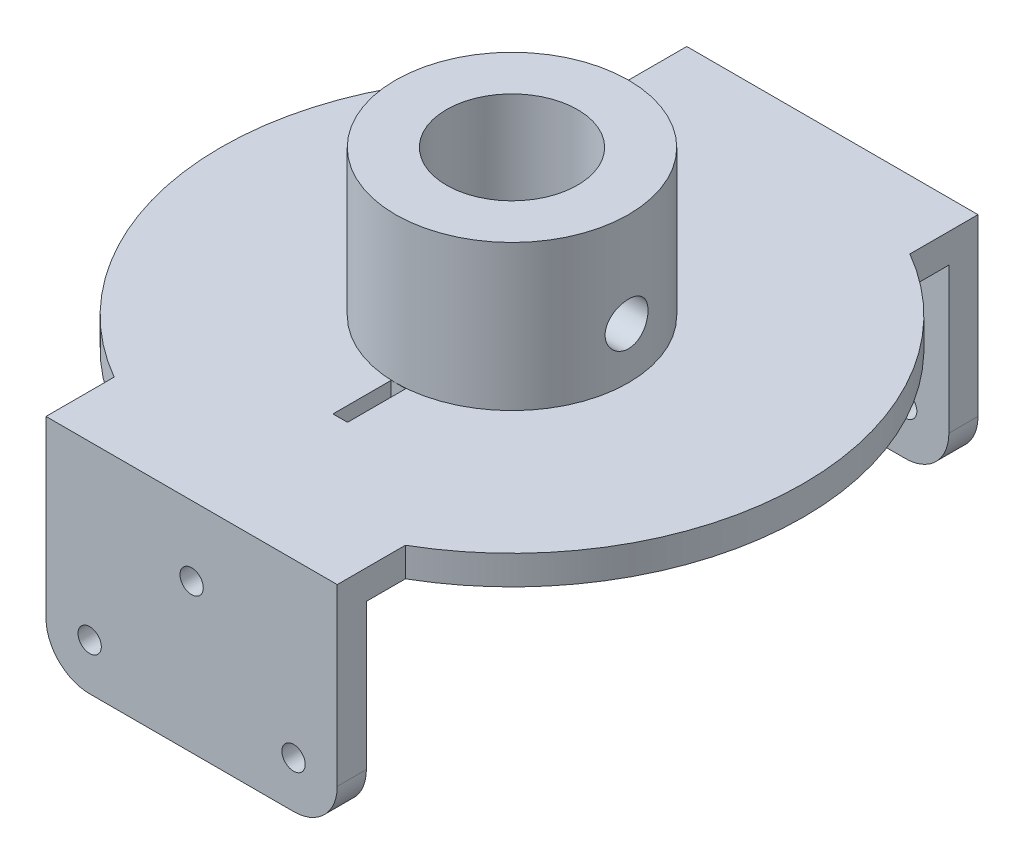
SolidWorks part; units mm, degrees
ref_plane "前视基准面" through (0, 0, 0) normal (0, 0, 1) x (1, 0, 0)
ref_plane "上视基准面" through (0, 0, 0) normal (0, 1, 0) x (1, 0, 0)
ref_plane "右视基准面" through (0, 0, 0) normal (1, 0, 0) x (0, 0, -1)
sketch "草图1" plane through (0, 0, 0) normal (0, 0, 1) x (1, 0, 0)
  line L0 (0, 0) -> (20, 0)
  line L5 (20, 0) -> (20, -13)
  line L6 (20, -13) -> (0, -13)
  line L7 (0, -13) -> (0, 0)
  line L8 (10, 0) -> (10, -2.8) construction
  circle A0 centre (10, -2.8) radius 0.8
  circle A1 centre (17, -9.8) radius 0.8
  circle A2 centre (3, -9.8) radius 0.8
  dimension "D1" = 14
  dimension "D4" = 1.6
  dimension "D5" = 1.6
  dimension "D2" = 20
  dimension "D3" = 7
  dimension "14" = 13
  dimension "D6" = 2.8
extrude "凸台-拉伸1" add sketch "草图1" along normal blind 2
sketch "草图2" plane through (0, 0, 0) normal (0, 1, 0) x (1, 0, 0)
  line L0 (0, 0) -> (0, -44)
  line L1 (0, -44) -> (20, -44)
  line L2 (20, -44) -> (20, 0)
  line L3 (20, 0) -> (0, 0)
extrude "凸台-拉伸2" add sketch "草图2" along normal blind 2
ref_plane "基准面4" through (0, 0, 22) normal (0, 0, 1) x (1, 0, 0)
mirror "镜向1" about plane through (0, 0, 22) normal (0, 0, 1) of "凸台-拉伸1"
sketch "草图3" plane through (0, 2, 0) normal (0, 1, 0) x (1, 0, 0)
  circle A0 centre (10, -22) radius 4.5
  circle A1 centre (10, -22) radius 8
extrude "凸台-拉伸3" add sketch "草图3" along normal blind 10
sketch "草图4" plane through (0, 2, 0) normal (0, 1, 0) x (1, 0, 0)
  circle A0 centre (10, -22) radius 20
extrude "凸台-拉伸4" add sketch "草图4" against normal blind 2 contours A0
ref_plane "基准面5" through (0, 5.5, 0) normal (0, 1, 0) x (1, 0, 0)
sketch "草图6" plane through (0, 5.5, 0) normal (0, 1, 0) x (1, 0, 0)
  line L0 (22.9766, -21.9965) -> (-13.4577, -21.9965) construction
  line L1 (0.1212, -21.9965) -> (0.1212, -20.5215)
  line L8 (0.1212, -20.5215) -> (20.2988, -20.5215)
  line L9 (20.2988, -20.5215) -> (20.2988, -21.9965)
  line L11 (0.1212, -21.9965) -> (20.2988, -21.9965)
revolve "切除-旋转1" cut sketch "草图6" angle 360 about L0
ref_plane "基准面6" through (0, 0, 34) normal (0, 0, 1) x (1, 0, 0)
sketch "草图7" plane through (0, 0, 34) normal (0, 0, 1) x (1, 0, 0)
  line L0 (9.7047, 2) -> (9.7047, -0.1272)
  line L1 (0, 2) -> (20, 2) construction
  line L2 (9.7047, -0.1272) -> (10.7047, -0.1272)
  line L3 (10.7047, -0.1272) -> (10.7047, 4.5788)
  line L4 (10.7047, 4.5788) -> (9.7047, 4.5788)
  line L5 (9.7047, 4.5788) -> (9.7047, 1.8811)
extrude "切除-拉伸1" cut sketch "草图7" against normal blind 4 contours L4 L5 L0 L2 L3
fillet "圆角1" radius 3 4 edges at (0, -13, 43) (20, -13, 43) (20, -13, 1) (0, -13, 1)
